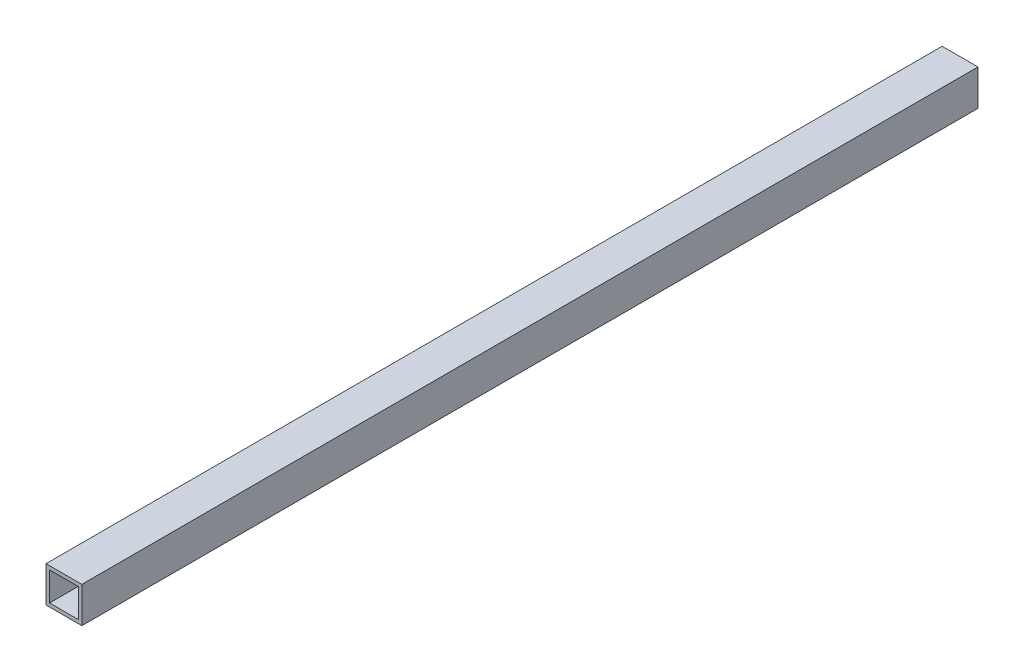
SolidWorks part; units mm, degrees
material "Alaşım Çelik"
ref_plane "Ön Düzlem" through (0, 0, 0) normal (0, 0, 1) x (1, 0, 0)
ref_plane "Üst Düzlem" through (0, 0, 0) normal (0, 1, 0) x (1, 0, 0)
ref_plane "Sağ Düzlem" through (0, 0, 0) normal (1, 0, 0) x (0, 0, -1)
sketch "Çizim1" plane through (0, 0, 0) normal (0, 0, 1) x (1, 0, 0)
  line L1 (0, 0) -> (40, 0)
  line L2 (0, 0) -> (0, 40)
  line L3 (0, 40) -> (40, 40)
  line L4 (40, 0) -> (40, 40)
  line L5 (4, 4) -> (36, 4)
  line L6 (4, 4) -> (4, 36)
  line L7 (4, 36) -> (36, 36)
  line L8 (36, 4) -> (36, 36)
  dimension "D1" = 40
  dimension "D2" = 40
  dimension "D3" = 4
  dimension "D4" = 4
  dimension "D5" = 4
  dimension "D6" = 4
extrude "Yükseklik-Ekstrüzyon1" add sketch "Çizim1" against normal blind 1000
